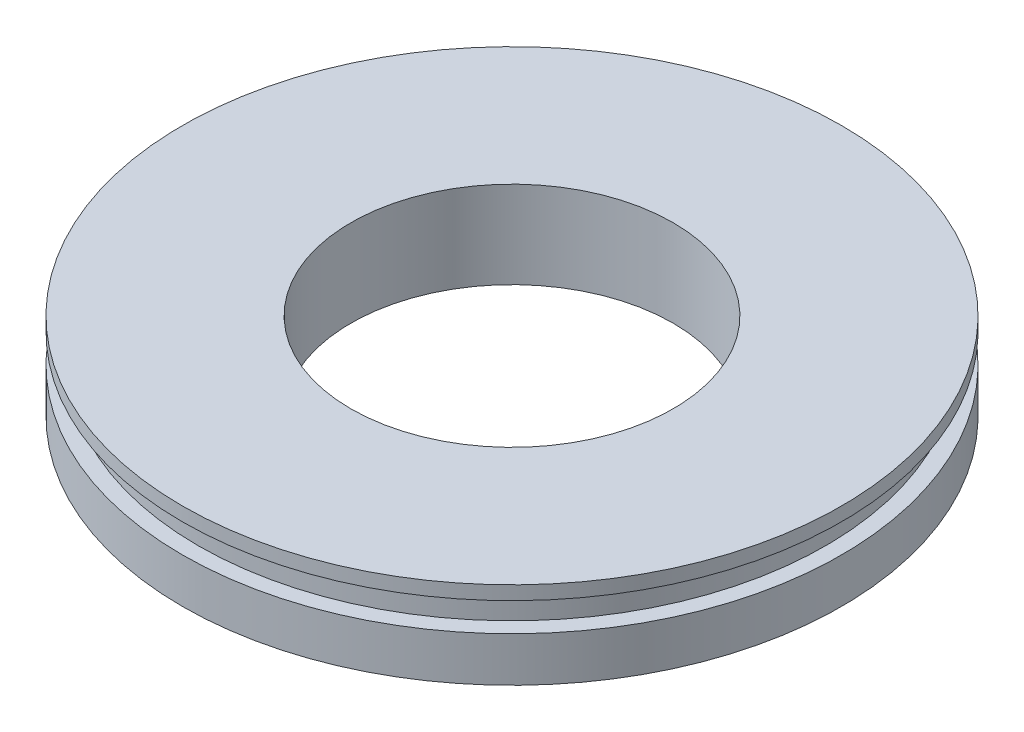
SolidWorks part; units mm, degrees
material "6061-T6 (SS)"
ref_plane "X-Y Datum" through (0, 0, 0) normal (0, 0, 1) x (1, 0, 0)
ref_plane "X-Z Datum" through (0, 0, 0) normal (0, 1, 0) x (1, 0, 0)
ref_plane "Y-Z Datum" through (0, 0, 0) normal (1, 0, 0) x (0, 0, -1)
sketch "Sketch1" plane through (0, 0, 0) normal (1, 0, 0) x (0, 0, -1)
  line L0 (-14.2875, 2.6941) -> (-14.2875, -5.0208)
  line L1 (-14.2875, -5.0208) -> (-29.21, -5.0208)
  line L3 (-29.21, -1.0621) -> (-27.8041, -1.0621)
  line L4 (-27.8041, -1.0621) -> (-27.8041, 1.4779)
  line L5 (-27.8041, 1.4779) -> (-29.21, 1.4779)
  line L6 (-29.21, 1.4779) -> (-29.21, 2.6941)
  line L7 (-29.21, 2.6941) -> (-14.2875, 2.6941)
  line L8 (0, 0) -> (0, -47872.0541) construction
  line L9 (0, 0) -> (-47872.0541, 0) construction
  line L10 (-29.21, -1.0621) -> (-29.21, -5.0208)
  line L11 (-15.0495, 2.6941) -> (14.7421, 2.6941) construction
  line L12 (-29.3688, 12.7) -> (-29.3687, -12.7) construction
  line L13 (14.2875, -5.0208) -> (-14.2875, -5.0208) construction
  line L14 (-29.3687, -1.0621) -> (29.3687, -1.0621) construction
  circle A0 centre (-28.6931, 0.2079) radius 0.889 construction
  point P15 (-29.3687, 0)
  point P16 (-27.8041, 0.2079)
  dimension "D3" = 1.778
  dimension "D1" = 28.575
  dimension "D2" = 58.42
  dimension "D4" = 2.54
  dimension "D5" = 25.4
  dimension "D6" = 58.7375
  dimension "D7" = 1.5646
revolve "Revolve1" add sketch "Sketch1" angle 360 about L8
